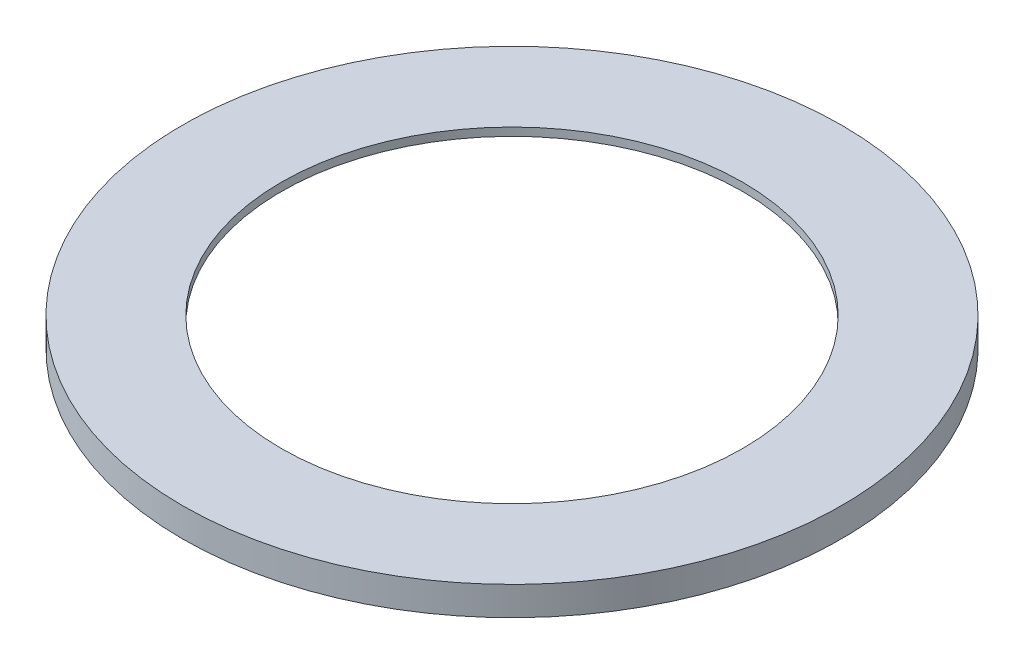
SolidWorks part; units mm, degrees
material "PVC Rigid"
ref_plane "Front" through (0, 0, 0) normal (0, 0, 1) x (1, 0, 0)
ref_plane "Top" through (0, 0, 0) normal (0, 1, 0) x (1, 0, 0)
ref_plane "Right" through (0, 0, 0) normal (1, 0, 0) x (0, 0, -1)
sketch "Sketch1" plane through (0, 0, 0) normal (0, 1, 0) x (1, 0, 0)
  circle A0 centre (0, 0) radius 40
  circle A1 centre (0, 0) radius 57.15
  dimension "D1" = 114.3
  dimension "D2" = 80
extrude "Boss-Extrude1" add sketch "Sketch1" along normal blind 5
sketch "Sketch2" plane through (0, 0, 0) normal (0, 0, 1) x (1, 0, 0)
  line L0 (0, 0) -> (40, 0) construction
  line L1 (40, 0) -> (40, 3.6)
  line L2 (40, 3.6) -> (57.15, 0)
  line L3 (57.15, 0) -> (40, 0)
  line L4 (0, 0) -> (0, 23.7803) construction
  dimension "D1" = 3.6
revolve "Cut-Revolve1" cut sketch "Sketch2" angle 360 about L4
